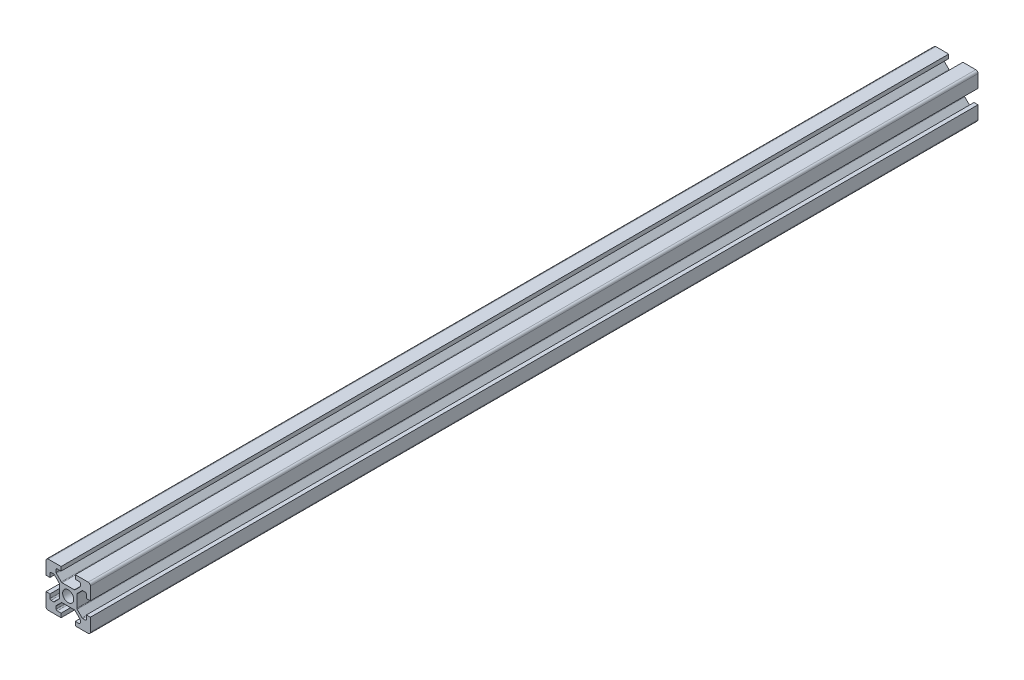
SolidWorks part; units mm, degrees
material "1060 Alloy"
ref_plane "Front Plane" through (0, 0, 0) normal (0, 0, 1) x (1, 0, 0)
ref_plane "Top Plane" through (0, 0, 0) normal (0, 1, 0) x (1, 0, 0)
ref_plane "Right Plane" through (0, 0, 0) normal (1, 0, 0) x (0, 0, -1)
sketch "Sketch1" plane through (0, 0, 0) normal (0, 0, 1) x (1, 0, 0)
  line L0 (20, 0) -> (-8.059, 28.059) construction
  line L1 (0, 0) -> (6.8, 0)
  line L2 (0, 0) -> (0, 6.8)
  line L3 (0, 20) -> (6.8, 20)
  line L4 (20, 0) -> (20, 6.8)
  line L5 (6.8, 20) -> (6.8, 18.2)
  line L6 (20, 20) -> (8.2322, 8.2322) construction
  line L7 (12.95, 6.1) -> (7.05, 6.1)
  line L8 (13.9, 7.05) -> (13.9, 12.95)
  line L9 (12.95, 13.9) -> (7.05, 13.9)
  line L10 (6.1, 7.05) -> (6.1, 12.95)
  line L11 (13.9, 6.1) -> (6.1, 13.9) construction
  line L12 (13.9, 13.9) -> (6.1, 6.1) construction
  line L13 (4.55, 16.4) -> (7.05, 13.9)
  line L14 (13.2, 18.2) -> (13.2, 20)
  line L15 (1.8, 6.8) -> (0, 6.8)
  line L16 (0, 13.2) -> (0, 20)
  line L17 (0, 13.2) -> (1.8, 13.2)
  line L18 (10, 10) -> (10, 13.9) construction
  line L19 (16.4, 4.55) -> (13.9, 7.05)
  line L20 (4.55, 16.4) -> (4.55, 18.2)
  line L21 (4.55, 18.2) -> (6.8, 18.2)
  line L22 (13.2, 18.2) -> (15.45, 18.2)
  line L23 (15.45, 18.2) -> (15.45, 16.4)
  line L24 (15.45, 16.4) -> (12.95, 13.9)
  line L25 (16.4, 4.55) -> (18.2, 4.55)
  line L26 (18.2, 4.55) -> (18.2, 6.8)
  line L27 (20, 6.8) -> (18.2, 6.8)
  line L28 (18.2, 13.2) -> (20, 13.2)
  line L29 (18.2, 13.2) -> (18.2, 15.45)
  line L30 (18.2, 15.45) -> (16.4, 15.45)
  line L31 (16.4, 15.45) -> (13.9, 12.95)
  line L32 (1.8, 4.55) -> (3.6, 4.55)
  line L33 (3.6, 15.45) -> (6.1, 12.95)
  line L34 (3.6, 15.45) -> (1.8, 15.45)
  line L35 (1.8, 15.45) -> (1.8, 13.2)
  line L36 (0, 13.2) -> (1.8, 13.2)
  line L37 (1.8, 6.8) -> (0, 6.8)
  line L38 (3.6, 4.55) -> (6.1, 7.05)
  line L39 (1.8, 6.8) -> (1.8, 4.55)
  line L40 (15.45, 3.6) -> (12.95, 6.1)
  line L41 (4.55, 3.6) -> (7.05, 6.1)
  line L42 (4.55, 1.8) -> (4.55, 3.6)
  line L43 (6.8, 1.8) -> (4.55, 1.8)
  line L44 (6.8, 1.8) -> (6.8, 0)
  line L45 (15.45, 3.6) -> (15.45, 1.8)
  line L46 (15.45, 1.8) -> (13.2, 1.8)
  line L47 (13.2, 0) -> (13.2, 1.8)
  line L48 (13.2, 20) -> (20, 20)
  line L49 (20, 13.2) -> (20, 20)
  line L50 (13.2, 0) -> (20, 0)
  line L51 (6.1, 6.1) -> (-5.5045, -5.5045) construction
  circle A0 centre (10, 10) radius 2.5
  point P25 (10, 16.4)
  point P39 (13.2, 19.1)
  point P46 (0.9, 6.8)
  dimension "D3" = 5
  dimension "D2" = 20
  dimension "D4" = 7.8
  dimension "D5" = 7.8
  dimension "D6" = 6.8
  dimension "D7" = 6.8
  dimension "D8" = 1.8
  dimension "D9" = 10.9
  dimension "D10" = 1.8
  dimension "D11" = 10.9
  dimension "D12" = 20
extrude "Boss-Extrude1" add sketch "Sketch1" along normal blind 400 contours L47 L50 L4 L27 L26 L25 L19 L8 L31 L30 L29 L28 L49 L48 L14 L22 L23 L24 L9 L13 L20 L21 L5 L3 L16 L17 L35 L34 L33 L10 L38 L32 L39 L15 L2 L1 L44 L43 L42 L41 L7 L40 L45 L46 A0
fillet "Fillet1" radius 1 4 edges at (20, 20, 200) (20, 0, 200) (0, 0, 200) (0, 20, 200)
fillet "Fillet2" radius 0.5 6 edges at (4.55, 18.2, 200) (4.55, 16.4, 200) (7.05, 13.9, 200) (15.45, 18.2, 200) (15.45, 16.4, 200) (12.95, 13.9, 200)
fillet "Fillet3" radius 0.5 6 edges at (18.2, 15.45, 200) (16.4, 15.45, 200) (13.9, 12.95, 200) (18.2, 4.55, 200) (13.9, 7.05, 200) (16.4, 4.55, 200)
fillet "Fillet4" radius 0.5 6 edges at (1.8, 15.45, 200) (3.6, 15.45, 200) (6.1, 12.95, 200) (3.6, 4.55, 200) (1.8, 4.55, 200) (6.1, 7.05, 200)
fillet "Fillet5" radius 0.5 6 edges at (7.05, 6.1, 200) (4.55, 3.6, 200) (4.55, 1.8, 200) (15.45, 1.8, 200) (15.45, 3.6, 200) (12.95, 6.1, 200)
